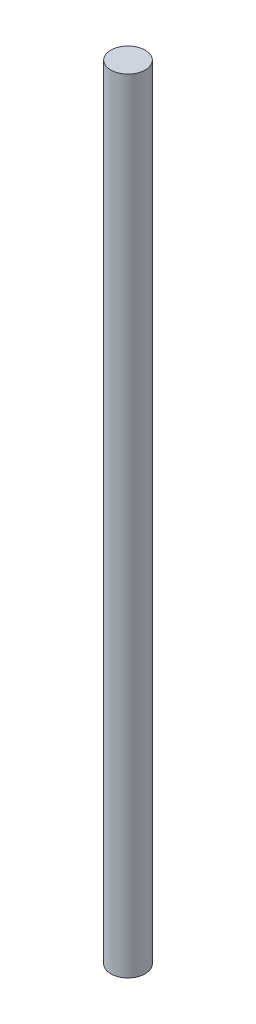
SolidWorks part; units mm, degrees
material "Chromium Copper, UNS C18200"
ref_plane "Front Plane" through (0, 0, 0) normal (0, 0, 1) x (1, 0, 0)
ref_plane "Top Plane" through (0, 0, 0) normal (0, 1, 0) x (1, 0, 0)
ref_plane "Right Plane" through (0, 0, 0) normal (1, 0, 0) x (0, 0, -1)
sketch "Sketch1" plane through (0, 0, 0) normal (0, 1, 0) x (1, 0, 0)
  circle A0 centre (0, 0) radius 1.8415
  dimension "D1" = 3.683
extrude "Boss-Extrude1" add sketch "Sketch1" along normal blind 83.693
cosmetic thread "Cosmetic Thread1" parameters "D1"=4.445, "D2"=2.5603
cosmetic thread "Cosmetic Thread2" parameters "D1"=4.445, "D2"=2.5603
